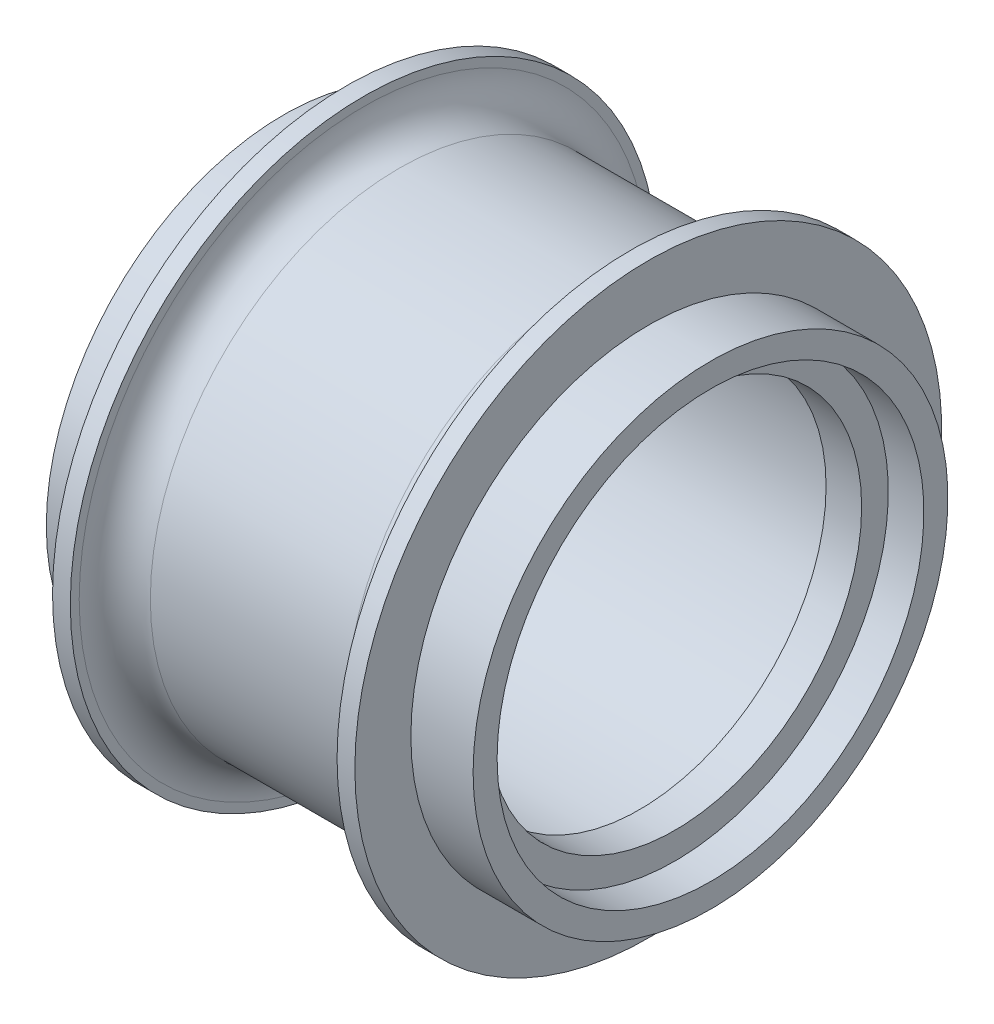
SolidWorks part; units mm, degrees
material "6061-T6 (SS)"
ref_plane "Płaszczyzna XY" through (0, 0, 0) normal (0, 0, 1) x (1, 0, 0)
ref_plane "Płaszczyzna XZ" through (0, 0, 0) normal (0, 1, 0) x (1, 0, 0)
ref_plane "Płaszczyzna YZ" through (0, 0, 0) normal (1, 0, 0) x (0, 0, -1)
sketch "Szkic1" plane through (0, 0, 0) normal (0, 0, 1) x (1, 0, 0)
  line L0 (-7.002, 0) -> (31.0108, 0) construction
  line L1 (-12, 12) -> (-9.3, 12)
  line L2 (-9.3, 12) -> (-9.3, 12.6)
  line L3 (-9.3, 12.6) -> (-8, 12.6)
  line L4 (-8, 12.6) -> (-8, 12)
  line L5 (-8, 12) -> (8, 12)
  line L6 (8, 12) -> (8, 10.5)
  line L7 (8, 10.5) -> (10, 10.5)
  line L8 (12, 12) -> (12, 13.35)
  line L9 (12, 13.35) -> (8.5, 13.35)
  line L10 (8.5, 13.35) -> (8.5, 16.5)
  line L11 (8.5, 16.5) -> (7.5, 16.5)
  line L12 (-12, 12) -> (-12, 13.35)
  line L13 (-12, 13.35) -> (-8.5, 13.35)
  line L14 (-8.5, 13.35) -> (-8.5, 16.5)
  line L15 (-8.5, 16.5) -> (-7.5, 16.5)
  line L16 (-7.5, 16.5) -> (-7.5, 16)
  line L17 (-5.5, 14) -> (5.5, 14)
  line L18 (7.5, 16) -> (7.5, 16.5)
  line L19 (10, 10.5) -> (10, 12)
  line L20 (10, 12) -> (12, 12)
  line L21 (0, 0) -> (0, 19.2409) construction
  arc A0 (5.5, 14) -> (7.5, 16) centre (5.5, 16) ccw
  arc A1 (-7.5, 16) -> (-5.5, 14) centre (-5.5, 16) ccw
  point P33 (0, 12)
  dimension "D11" = 2
  dimension "D2" = 16
  dimension "D3" = 24
  dimension "D4" = 1.3
  dimension "D5" = 28
  dimension "D6" = 3.5
  dimension "D7" = 3.5
  dimension "D8" = 1
  dimension "D9" = 1
  dimension "D10" = 33
  dimension "D12" = 21
  dimension "D13" = 25.2
  dimension "D14" = 24
  dimension "D15" = 26.7
  dimension "D18" = 2
revolve "Obrót1" add sketch "Szkic1" angle 360 about L0
